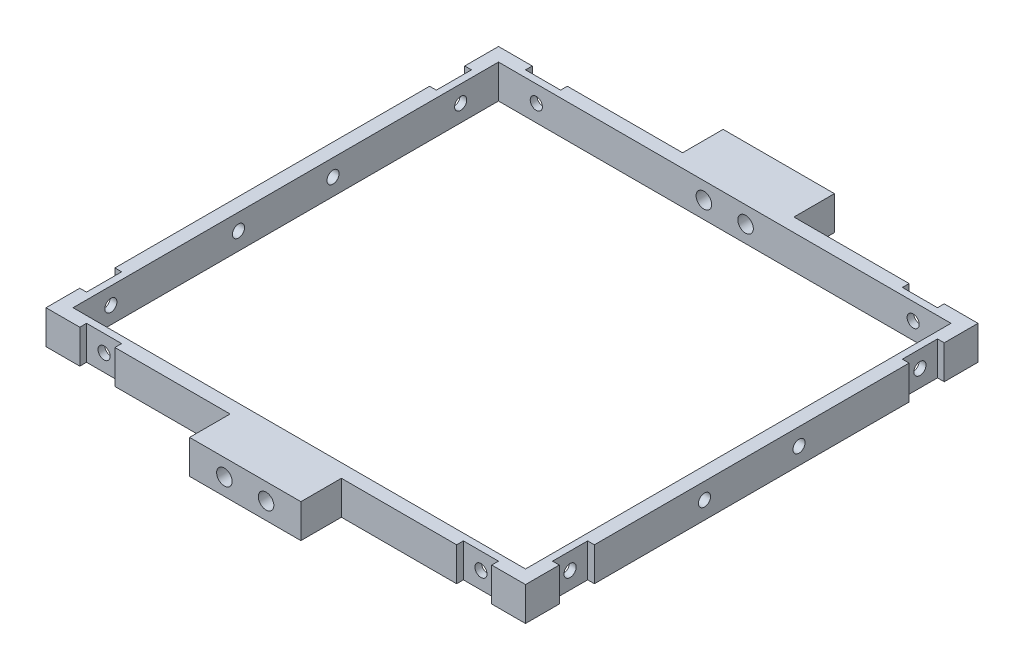
SolidWorks part; units mm, degrees
ref_plane "Front Plane" through (0, 0, 0) normal (0, 0, 1) x (1, 0, 0)
ref_plane "Top Plane" through (0, 0, 0) normal (0, 1, 0) x (1, 0, 0)
ref_plane "Right Plane" through (0, 0, 0) normal (1, 0, 0) x (0, 0, -1)
sketch "Sketch1" plane through (0, 0, 0) normal (0, 1, 0) x (1, 0, 0)
  line L1 (-35.5, 33.5) -> (35.5, 33.5)
  line L2 (-35.5, 33.5) -> (-35.5, -33.5)
  line L3 (-35.5, -33.5) -> (35.5, -33.5)
  line L4 (35.5, 33.5) -> (35.5, -33.5)
  line L5 (-35.5, 33.5) -> (35.5, -33.5) construction
  line L6 (-35.5, -33.5) -> (35.5, 33.5) construction
  line L7 (-33.5, 31.5) -> (33.5, 31.5)
  line L8 (-33.5, 31.5) -> (-33.5, -31.5)
  line L9 (-33.5, -31.5) -> (33.5, -31.5)
  line L10 (33.5, 31.5) -> (33.5, -31.5)
  line L11 (-33.5, 31.5) -> (33.5, -31.5) construction
  line L12 (-33.5, -31.5) -> (33.5, 31.5) construction
  point P0 (0, 0)
  point P6 (0, 0)
  dimension "D1" = 67
  dimension "D2" = 71
  dimension "D3" = 2
  dimension "D4" = 2
extrude "Boss-Extrude1" add sketch "Sketch1" along normal blind 5
sketch "Sketch2" plane through (35.5, 0, 0) normal (1, 0, 0) x (0, 0, -1)
  line L1 (-33.5, 5) -> (33.5, 5) construction
  circle A0 centre (-6.9997, 2.5914) radius 0.9
  circle A1 centre (7, 2.5) radius 0.9
  dimension "D1" = 14
  dimension "D2" = 2.5
  dimension "D3" = 7
  dimension "D4" = 1.8
  dimension "D5" = 1.8
  dimension "D6" = 6.9997
extrude "Cut-Extrude1" cut sketch "Sketch2" against normal blind 121
sketch "Sketch3" plane through (0, 0, 33.5) normal (0, 0, 1) x (1, 0, 0)
  line L0 (-35.5, 5) -> (35.5, 5) construction
  circle A0 centre (0, 2.5) radius 1
  dimension "D1" = 2
  dimension "D2" = 2.5
  dimension "D3" = 0
extrude "Cut-Extrude2" cut sketch "Sketch3" against normal blind 0.01
sketch "Sketch4" plane through (0, 0, 33.5) normal (0, 0, 1) x (1, 0, 0)
  line L0 (-35.5, 0) -> (35.5, 0) construction
  line L1 (3.425, 5) -> (7.425, 5)
  line L2 (3.425, 5) -> (3.425, 0)
  line L3 (3.425, 0) -> (7.425, 0)
  line L4 (7.425, 5) -> (7.425, 0)
  line L7 (-3.4289, 5) -> (-7.4289, 5)
  line L8 (-3.4289, 5) -> (-3.4289, 0)
  line L9 (-3.4289, 0) -> (-7.4289, 0)
  line L10 (-7.4289, 5) -> (-7.4289, 0)
  dimension "D1" = 4
  dimension "D2" = 4
  dimension "D3" = 5
  dimension "D4" = 5
  dimension "D5" = 6.8539
  dimension "D6" = 0
  dimension "D7" = 0
  dimension "D8" = 3.425
ref_plane "Plane1" through (0, 0, 0) normal (0, 0, 1) x (1, 0, 0)
sketch "Sketch9" plane through (0, 0, 33.5) normal (0, 0, 1) x (1, 0, 0)
  line L0 (-35.5, 5) -> (35.5, 5) construction
  line L1 (-30.5, 5) -> (-25.3, 5)
  line L2 (-30.5, 5) -> (-30.5, 0)
  line L3 (-30.5, 0) -> (-25.3, 0)
  line L4 (-25.3, 5) -> (-25.3, 0)
  line L5 (-35.5, 0) -> (35.5, 0) construction
  line L6 (-35.5, 0) -> (35.5, 0) construction
  line L7 (30.5, 5) -> (25.3, 5)
  line L8 (30.5, 5) -> (30.5, 0)
  line L9 (30.5, 0) -> (25.3, 0)
  line L10 (25.3, 5) -> (25.3, 0)
  line L11 (-35.5, 5) -> (-35.5, 0) construction
  line L12 (35.5, 5) -> (35.5, 0) construction
  dimension "D1" = 5.2
  dimension "D2" = 5
  dimension "D3" = 5
  dimension "D4" = 5.2
extrude "Cut-Extrude6" cut sketch "Sketch9" against normal blind 1
sketch "Sketch10" plane through (35.5, 0, 0) normal (1, 0, 0) x (0, 0, -1)
  line L0 (-33.5, 5) -> (33.5, 5) construction
  line L1 (-28.5, 5) -> (-23.3, 5)
  line L2 (-28.5, 5) -> (-28.5, 0)
  line L3 (-28.5, 0) -> (-23.3, 0)
  line L4 (-23.3, 5) -> (-23.3, 0)
  line L5 (-33.5, 0) -> (33.5, 0) construction
  line L6 (33.5, 5) -> (33.5, 0) construction
  line L7 (28.5, 5) -> (23.3, 5)
  line L8 (28.5, 5) -> (28.5, 0)
  line L9 (28.5, 0) -> (23.3, 0)
  line L10 (23.3, 5) -> (23.3, 0)
  line L11 (-33.5, 5) -> (-33.5, 0) construction
  dimension "D1" = 5.2
  dimension "D2" = 5.2
  dimension "D3" = 5
  dimension "D4" = 5
extrude "Cut-Extrude7" cut sketch "Sketch10" against normal blind 1
ref_plane "Plane2" through (0, 0, 0) normal (1, 0, 0) x (0, 0, -1)
mirror "Mirror2" about plane through (0, 0, 0) normal (1, 0, 0) of "Cut-Extrude7"
mirror "Mirror3" about plane through (0, 0, 0) normal (0, 0, 1) of "Cut-Extrude6"
sketch "Sketch11" plane through (34.5, 0, 0) normal (1, 0, 0) x (0, 0, -1)
  circle A0 centre (25.9, 2.5) radius 0.9
  circle A1 centre (-25.9, 2.5) radius 0.9
  dimension "D1" = 1.8
  dimension "D2" = 1.8
extrude "Cut-Extrude8" cut sketch "Sketch11" against normal blind 81
sketch "Sketch12" plane through (0, 0, 32.5) normal (0, 0, 1) x (1, 0, 0)
  circle A0 centre (27.9, 2.5) radius 0.9
  circle A1 centre (-27.9, 2.5) radius 0.9
  dimension "D1" = 1.8
  dimension "D2" = 1.8
extrude "Cut-Extrude9" cut sketch "Sketch12" against normal blind 81
sketch "Sketch13" plane through (0, 0, 0) normal (0, 0, 1) x (1, 0, 0)
  circle A0 centre (-1.2814, -41.6511) radius 1.15
  circle A1 centre (4.8918, -41.6511) radius 1.15
  dimension "D1" = 2.3
  dimension "D2" = 2.3
sketch "Sketch14" plane through (0, 0, -33.5) normal (0, 0, -1) x (-1, 0, 0)
  line L0 (0, 2.75) -> (0, -2.75) construction
  circle A0 centre (-3.085, 2.5) radius 1.15
  circle A1 centre (3.0882, 2.5) radius 1.15
  circle A2 centre (0, 2.5) radius 1 construction
  dimension "D1" = 6.1732
  dimension "D2" = 2.3
  dimension "D3" = 2.3
  dimension "D5" = 0
  dimension "D6" = 0
  dimension "D4" = 3.085
extrude "Cut-Extrude10" cut sketch "Sketch14" against normal blind 79
sketch "Sketch15" plane through (0, 0, -33.5) normal (0, 0, -1) x (-1, 0, 0)
  line L0 (-25.3, 0) -> (25.3, 0) construction
  line L1 (-8.2417, 5) -> (8.2417, 5)
  line L2 (-8.2417, 5) -> (-8.2417, 0)
  line L3 (-8.2417, 0) -> (8.2417, 0)
  line L4 (8.2417, 5) -> (8.2417, 0)
  line L5 (-8.2417, 5) -> (8.2417, 0) construction
  line L6 (-8.2417, 0) -> (8.2417, 5) construction
  point P0 (0, 2.5)
extrude "Boss-Extrude2" add sketch "Sketch15" along normal blind 6
sketch "Sketch16" plane through (0, 0, -31.5) normal (0, 0, 1) x (1, 0, 0)
  circle A0 centre (-3.0882, 2.5) radius 1.15
  circle A1 centre (3.085, 2.5) radius 1.15
extrude "Cut-Extrude11" cut sketch "Sketch16" against normal blind 30
mirror "Mirror4" about plane through (0, 0, 0) normal (0, 0, 1) of "Boss-Extrude2", "Cut-Extrude10"
sketch "Sketch17" plane through (0, 0, 31.5) normal (0, 0, -1) x (-1, 0, 0)
  circle A0 centre (-3.085, 2.5) radius 1.15
  circle A1 centre (3.0882, 2.5) radius 1.15
extrude "Cut-Extrude12" cut sketch "Sketch17" against normal blind 30
